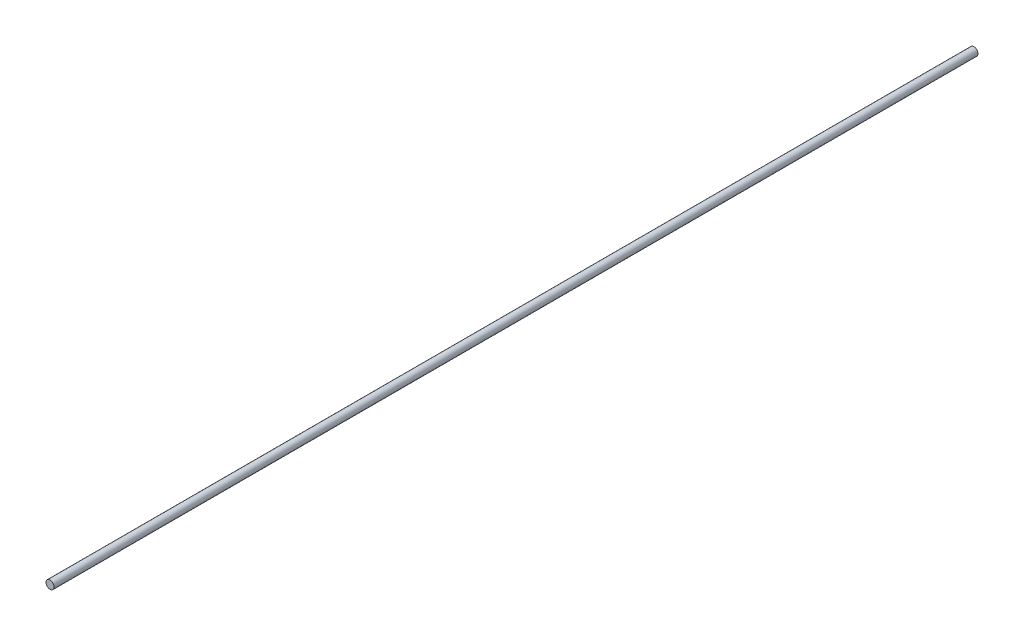
SolidWorks part; units mm, degrees
material "Stainless Steel (ferritic)"
ref_plane "Front Plane" through (0, 0, 0) normal (0, 0, 1) x (1, 0, 0)
ref_plane "Top Plane" through (0, 0, 0) normal (0, 1, 0) x (1, 0, 0)
ref_plane "Right Plane" through (0, 0, 0) normal (1, 0, 0) x (0, 0, -1)
sketch "Sketch1" plane through (0, 0, 0) normal (0, 0, 1) x (1, 0, 0)
  circle A0 centre (0, 0) radius 4
  dimension "D1" = 8
extrude "Boss-Extrude1" add sketch "Sketch1" along normal blind 914.4
